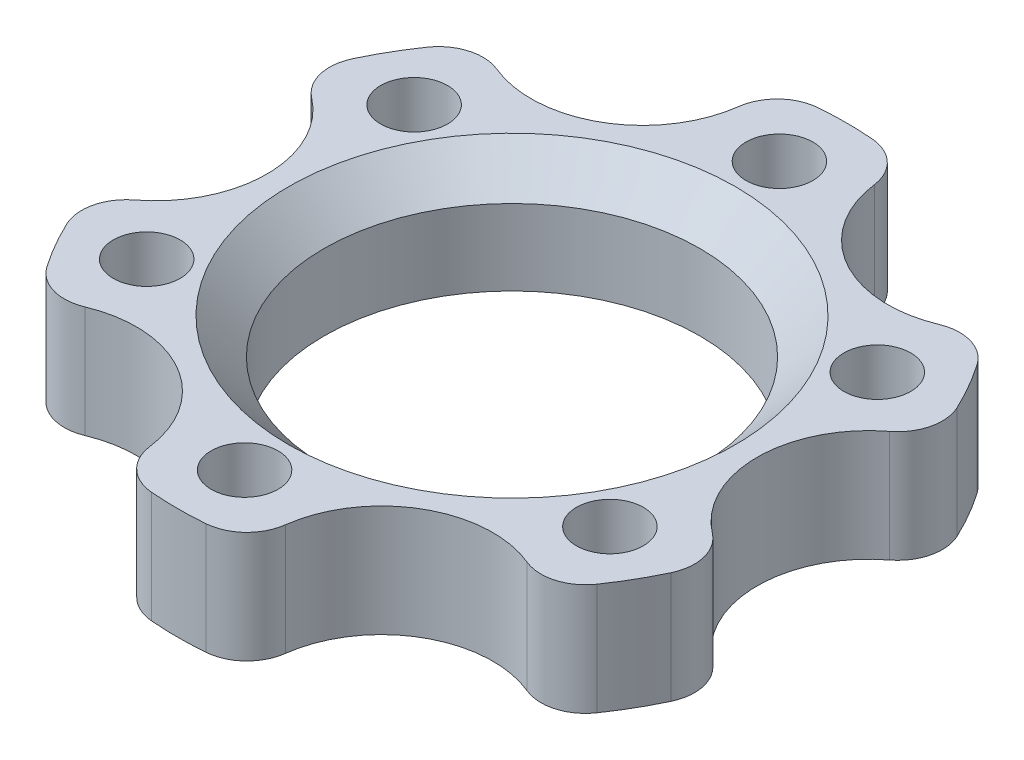
SolidWorks part; units mm, degrees
material "6061-T6 (SS)"
ref_plane "Front Plane" through (0, 0, 0) normal (0, 0, 1) x (1, 0, 0)
ref_plane "Top Plane" through (0, 0, 0) normal (0, 1, 0) x (1, 0, 0)
ref_plane "Right Plane" through (0, 0, 0) normal (1, 0, 0) x (0, 0, -1)
sketch "Sketch1" plane through (0, 0, 0) normal (0, 0, 1) x (1, 0, 0)
  line L0 (0, 0) -> (25.4898, 0) construction
  line L1 (25.4898, 0) -> (31.8398, 6.35)
  line L2 (31.8398, 6.35) -> (47.625, 6.35)
  line L3 (47.625, 6.35) -> (47.625, 0)
  line L4 (47.625, 0) -> (25.4898, 0)
  line L5 (33.917, 8.517) -> (25.4, 0)
  line L6 (26.7598, 1.27) -> (26.7598, 0)
  line L7 (0, 0) -> (0, 15.0405) construction
  line L8 (26.7598, 0) -> (26.7598, -9.525)
  line L9 (26.7598, -9.525) -> (47.625, -9.525)
  line L10 (47.625, -9.525) -> (47.625, 0)
  dimension "D1" = 135
  dimension "D2" = 0.0635
  dimension "D3" = 25.4
  dimension "D4" = 1.27
  dimension "D5" = 47.625
  dimension "D6" = 6.35
  dimension "D7" = 15.875
revolve "Revolve1" add sketch "Sketch1" angle 360 about L7
sketch "Sketch2" plane through (0, 6.35, 0) normal (0, -1, 0) x (-1, 0, 0)
  line L0 (0, 0) -> (0, 38.1) construction
  line L1 (0, 0) -> (50.8, 0) construction
  circle A0 centre (0, 38.1) radius 4.7625
  circle A10 centre (32.9956, 19.05) radius 4.7625
  circle A11 centre (32.9956, -19.05) radius 4.7625
  circle A12 centre (0, -38.1) radius 4.7625
  circle A13 centre (-32.9956, -19.05) radius 4.7625
  circle A14 centre (-32.9956, 19.05) radius 4.7625
  circle A15 centre (50.8, 0) radius 15.875
  circle A16 centre (25.4, -43.9941) radius 15.875
  circle A17 centre (-25.4, -43.9941) radius 15.875
  circle A18 centre (-50.8, 0) radius 15.875
  circle A19 centre (-25.4, 43.9941) radius 15.875
  circle A20 centre (25.4, 43.9941) radius 15.875
  point P16 (0, 0)
  point P20 (0, 0)
  point P26 (0, 0)
  point P32 (0, 0)
  dimension "D2" = 9.525
  dimension "D5" = 31.75
  dimension "D1" = 38.1
  dimension "D4" = 50.8
  dimension "D3" = 6
  dimension "D6" = 6
extrude "Cut-Extrude1" cut sketch "Sketch2" against normal through all and the other way through all
fillet "Fillet1" radius 6.35 12 edges at (-35.5005, -1.5875, 31.7468) (-9.7433, -1.5875, 46.6177) (-45.2437, -1.5875, -14.8709) (-45.2437, -1.5875, 14.8709) (9.7433, -1.5875, 46.6177) (35.5005, -1.5875, 31.7468) (45.2437, -1.5875, 14.8709) (45.2437, -1.5875, -14.8709) (35.5005, -1.5875, -31.7468) (9.7433, -1.5875, -46.6177) (-9.7433, -1.5875, -46.6177) (-35.5005, -1.5875, -31.7468)
